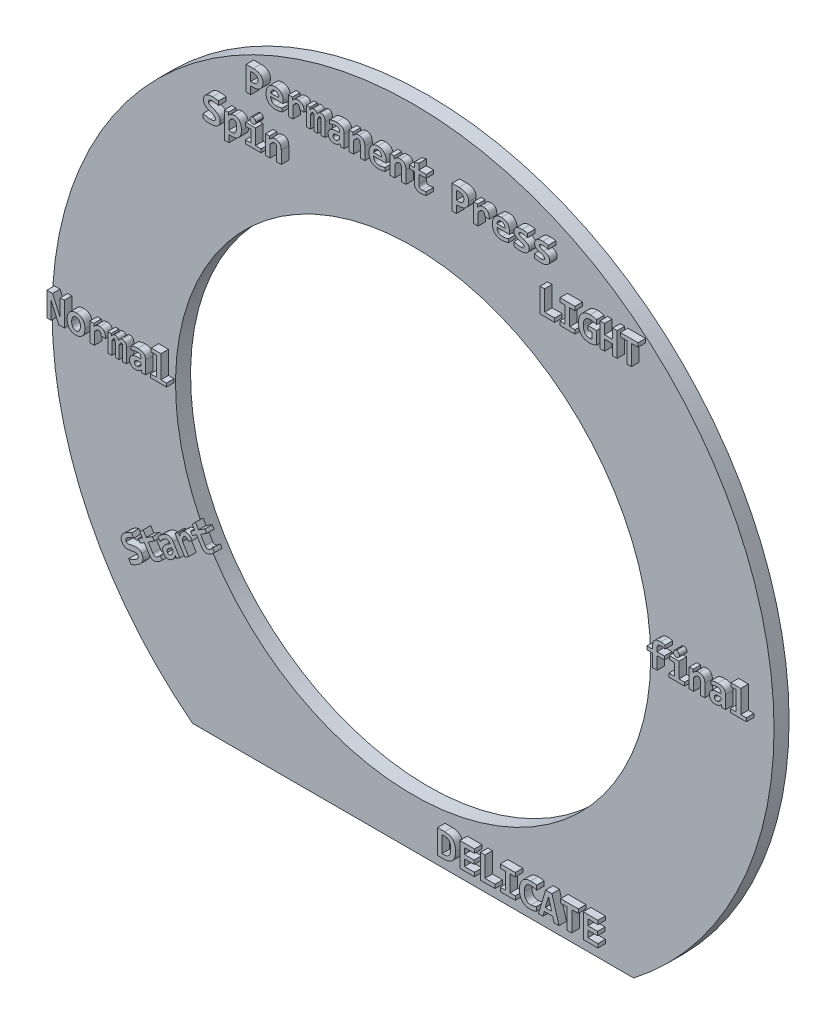
SolidWorks part; units mm, degrees
ref_plane "Front Plane" through (0, 0, 0) normal (0, 0, 1) x (1, 0, 0)
ref_plane "Top Plane" through (0, 0, 0) normal (0, 1, 0) x (1, 0, 0)
ref_plane "Right Plane" through (0, 0, 0) normal (1, 0, 0) x (0, 0, -1)
sketch "Sketch1" plane through (0, 0, 0) normal (0, 0, 1) x (1, 0, 0)
  line L0 (-46.5546, -60.325) -> (46.5546, -60.325)
  line L1 (-504.825, -66.675) -> (130.175, -66.675) construction
  arc A0 (46.5546, -60.325) -> (-46.5546, -60.325) centre (0, 0) ccw
  circle A1 centre (0, 0) radius 38.1 construction
  circle A2 centre (0, 0) radius 50.1538
  dimension "D1" = 152.4
  dimension "D2" = 6.35
extrude "Plate" add sketch "Sketch1" along normal blind 3.175
sketch "Sketch3" plane through (0, 0, 3.175) normal (0, 0, 1) x (1, 0, 0)
  line L0 (6.3719, -57.0243) -> (39.5287, -57.0243) construction
  line L1 (-76.0772, 0) -> (-50.665, 0) construction
  line L2 (50.665, 0) -> (76.2, 0) construction
  line L3 (-34.1531, 62.3168) -> (29.0102, 62.3168) construction
  line L4 (-43.1001, 52.7834) -> (-28.9064, 52.7834) construction
  line L5 (27.6576, 52.7834) -> (46.9482, 52.7834) construction
  line L6 (-45.9948, -53.8666) -> (-34.1531, -53.8666) construction
  line L7 (-58.2257, -36.4627) -> (-42.9401, -26.8904) construction
  circle A0 centre (0, 0) radius 50.665 construction
  circle A1 centre (0, 0) radius 38.1 construction
  arc A2 (46.5546, -60.325) -> (-46.5546, -60.325) centre (0, 0) ccw construction
  text T0 "Permanent Press"
  text T1 "Spin"
  text T2 "LIGHT"
  text T3 "Normal"
  text T4 "final rinse"
  text T5 "DELICATES"
  text T6 "Start"
extrude "Letteriing" add sketch "Sketch3" along normal blind 1.5875
